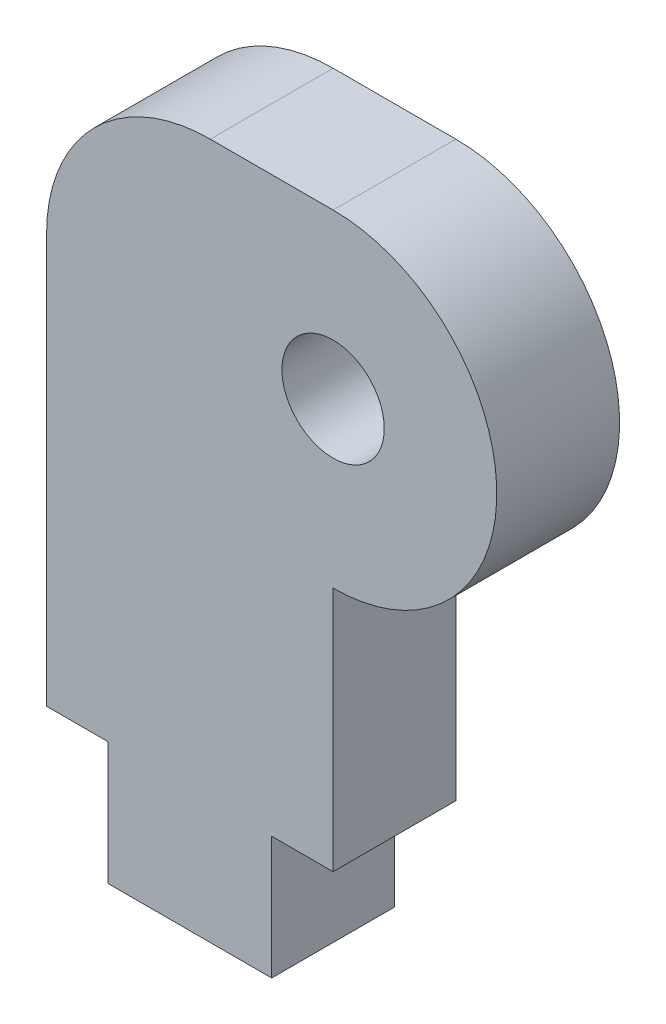
SolidWorks part; units mm, degrees
ref_plane "Front Plane" through (0, 0, 0) normal (0, 0, 1) x (1, 0, 0)
ref_plane "Top Plane" through (0, 0, 0) normal (0, 1, 0) x (1, 0, 0)
ref_plane "Right Plane" through (0, 0, 0) normal (1, 0, 0) x (0, 0, -1)
sketch "Sketch1" plane through (0, 0, 0) normal (0, 0, 1) x (1, 0, 0)
  line L0 (0, 26.9507) -> (0, -40.519) construction
  line L1 (-7, 4) -> (-7, -10)
  line L2 (-7, -10) -> (-5.5, -10)
  line L3 (-5.5, -10) -> (-5.5, -13)
  line L4 (-5.5, -13) -> (-1.5, -13)
  line L5 (-1.5, -13) -> (-1.5, -10)
  line L6 (-1.5, -10) -> (0, -10)
  line L7 (0, -10) -> (0, -4)
  line L8 (0, 4) -> (-7, 4)
  line L10 (-7, 26.9507) -> (-7, -40.519) construction
  arc A0 (0, -4) -> (0, 4) centre (0, 0) ccw
  circle A1 centre (0, 0) radius 1.25
  dimension "D2" = 8
  dimension "D3" = 0
  dimension "2.5" = 2.5
  dimension "14" = 14
  dimension "D6" = 1.5
  dimension "D7" = 3
  dimension "D8" = 4
  dimension "D1" = 7
extrude "Boss-Extrude1" add sketch "Sketch1" along normal blind 3
fillet "Fillet1" radius 4 1 edges at (-7, 4, 1.5)
